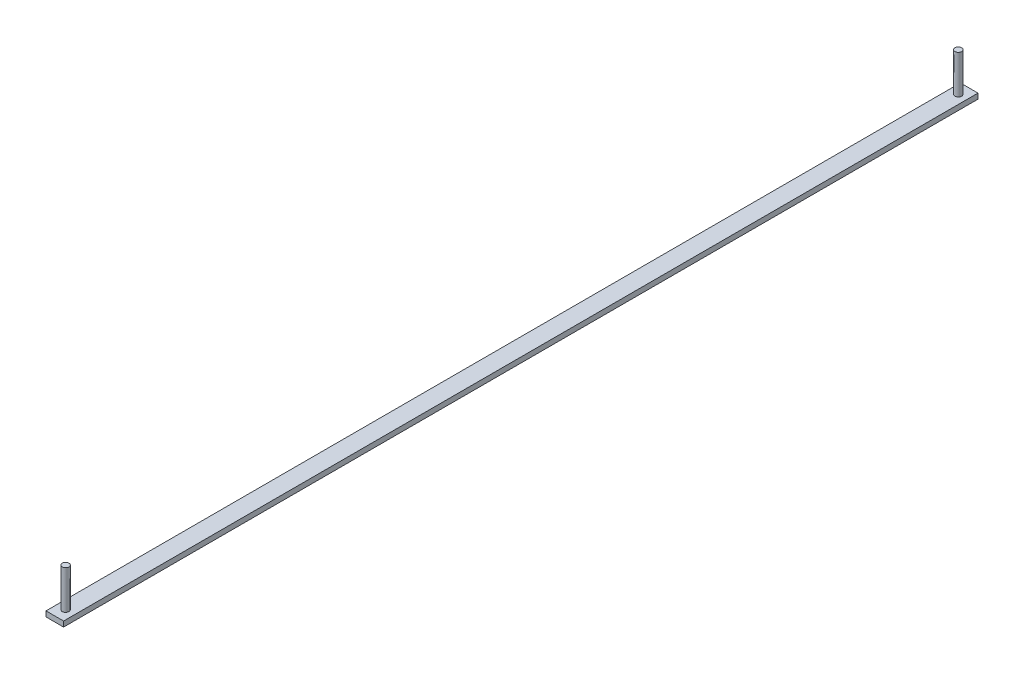
SolidWorks part; units mm, degrees
ref_plane "Front Plane" through (0, 0, 0) normal (0, 0, 1) x (1, 0, 0)
ref_plane "Top Plane" through (0, 0, 0) normal (0, 1, 0) x (1, 0, 0)
ref_plane "Right Plane" through (0, 0, 0) normal (1, 0, 0) x (0, 0, -1)
sketch "Sketch1" plane through (0, 0, 0) normal (0, 1, 0) x (1, 0, 0)
  line L1 (0, 0) -> (25.4, 0)
  line L2 (0, 0) -> (0, 1320.8)
  line L3 (0, 1320.8) -> (25.4, 1320.8)
  line L4 (25.4, 0) -> (25.4, 1320.8)
  dimension "D1" = 25.4
  dimension "D2" = 1320.8
extrude "Boss-Extrude1" add sketch "Sketch1" along normal blind 7.62
sketch "Sketch2" plane through (0, 7.62, 0) normal (0, 1, 0) x (1, 0, 0)
  circle A0 centre (12.7, 15.621) radius 4.826
  circle A1 centre (12.7, 1305.052) radius 4.826
  dimension "D2" = 9.652
  dimension "D3" = 9.652
  dimension "D1" = 1289.431
extrude "Boss-Extrude2" add sketch "Sketch2" along normal blind 55.88
